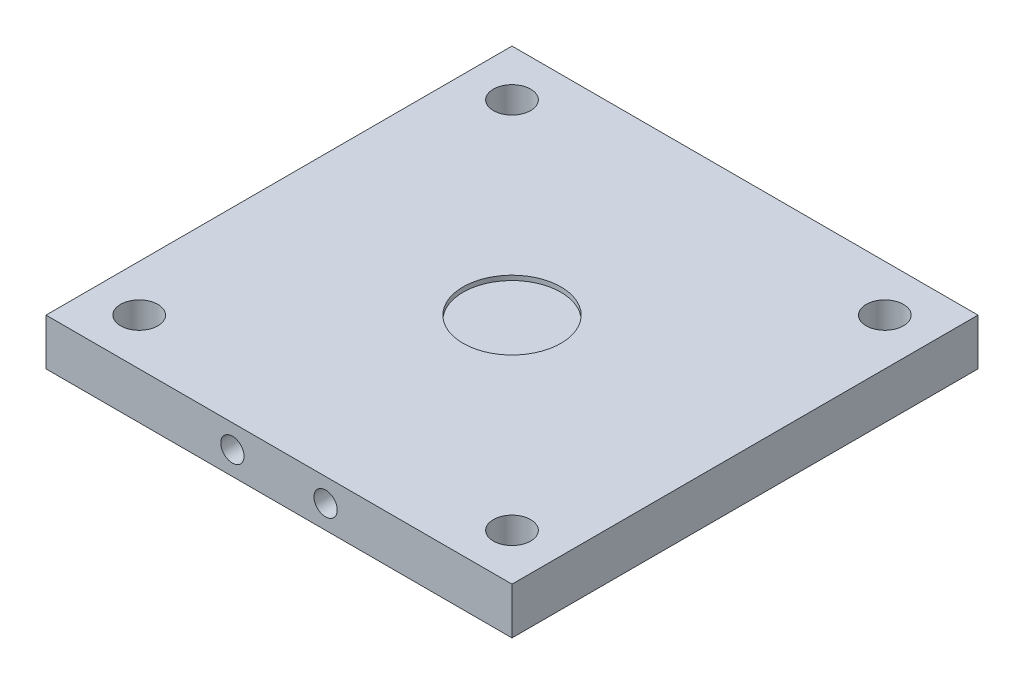
SolidWorks part; units mm, degrees
material "6061-T4 (SS)"
ref_plane "Front Plane" through (0, 0, 0) normal (0, 0, 1) x (1, 0, 0)
ref_plane "Top Plane" through (0, 0, 0) normal (0, 1, 0) x (1, 0, 0)
ref_plane "Right Plane" through (0, 0, 0) normal (1, 0, 0) x (0, 0, -1)
sketch "Sketch1" plane through (0, 0, 0) normal (0, 1, 0) x (1, 0, 0)
  line L1 (50, 50) -> (-50, 50)
  line L2 (50, 50) -> (50, -50)
  line L3 (50, -50) -> (-50, -50)
  line L4 (-50, 50) -> (-50, -50)
  line L5 (50, 50) -> (-50, -50) construction
  line L6 (50, -50) -> (-50, 50) construction
  point P0 (0, 0)
  dimension "D1" = 100
  dimension "D2" = 100
extrude "base" add sketch "Sketch1" along normal blind 10
sketch "Sketch2" plane through (0, 10, 0) normal (0, 1, 0) x (1, 0, 0)
  circle A0 centre (0, 0) radius 10.5
  dimension "D1" = 21
extrude "load cell cut" cut sketch "Sketch2" against normal blind 1 contours A0
sketch "post positioning points" plane through (0, 10, 0) normal (0, 1, 0) x (1, 0, 0)
  line L0 (-50, 50) -> (-50, -50) construction
  line L1 (-50, -50) -> (50, -50) construction
  line L2 (50, -50) -> (50, 50) construction
  line L3 (50, 50) -> (-50, 50) construction
  point P0 (-10, -40)
  point P5 (50, 40)
  point P6 (-10, 40)
  point P7 (10, 40)
  point P8 (10, -40)
  point P9 (75, -40)
  point P10 (-50, 40)
  dimension "D1" = 40
  dimension "D2" = 10
  dimension "D3" = 40
  dimension "D4" = 10
  dimension "D5" = 85
  dimension "D7" = 60
  dimension "D6" = 60
sketch "Sketch6" plane through (0, 0, -50) normal (0, 0, 1) x (1, 0, 0)
  line L0 (-50, 0) -> (50, 0) construction
  line L1 (9, 10) -> (-9, 10)
  line L2 (9, 10) -> (9, 5)
  line L3 (9, 5) -> (-9, 5)
  line L4 (-9, 10) -> (-9, 5)
  line L5 (9, 10) -> (-9, 5) construction
  line L6 (9, 5) -> (-9, 10) construction
  line L7 (-50, 10) -> (50, 10) construction
  point P0 (0, 7.5)
  point P8 (0, 0)
  dimension "D1" = 18
  dimension "D2" = 5
extrude "cut wire" [suppressed] cut sketch "Sketch6" along normal blind 50 contours L4 L3 L2 L1
sketch "Sketch7" plane through (0, 0, -50) normal (0, 0, 1) x (1, 0, 0)
  line L1 (5, 10) -> (-5, 10)
  line L2 (5, 10) -> (5, 0)
  line L3 (5, 0) -> (-5, 0)
  line L4 (-5, 10) -> (-5, 0)
  line L5 (5, 10) -> (-5, 0) construction
  line L6 (5, 0) -> (-5, 10) construction
  line L7 (-50, 0) -> (50, 0) construction
  line L8 (-50, 10) -> (50, 10) construction
  point P0 (0, 5)
  point P8 (0, 0)
  dimension "D1" = 10
  dimension "D2" = 10
extrude "cut wire 2" [suppressed] cut sketch "Sketch7" along normal up to next
fillet "Fillet5" [suppressed] radius 10
fillet "Fillet6" [suppressed] radius 0.1
fillet "Fillet7" [suppressed] radius 5
sketch "Sketch12" plane through (0, 0, 0) normal (0, -1, 0) x (1, 0, 0)
  line L0 (0, 0) -> (50, 0) construction
  line L1 (19.771, 8.1894) -> (-8.1894, 19.771) construction
  line L2 (-8.1894, 19.771) -> (-19.771, -8.1894) construction
  line L3 (-19.771, -8.1894) -> (8.1894, -19.771) construction
  line L4 (8.1894, -19.771) -> (19.771, 8.1894) construction
  line L5 (50, 50) -> (50, -50) construction
  circle A0 centre (0, 0) radius 15.1321 construction
  dimension "D1" = 22.5
  dimension "D2" = 21.4
hole_wizard "Ø5.0mm Dowel Hole1" [suppressed] positions "3DSketch4" profile "Sketch13" hole size "Ø5.0" standard "ANSI Metric"
sketch3d "3DSketch4"
  point P0 (-8.1894, 0, 19.771)
  point P3 (19.771, 0, 8.1894)
  point P6 (8.1894, 0, -19.771)
  point P9 (-19.771, 0, -8.1894)
sketch "Sketch13" plane through (-8.1894, 0, 19.771) normal (1, 0, 0) x (0, 0, -1)
  line L0 (0, 0) -> (0, 5)
  line L1 (0, 5) -> (2.5, 5)
  line L2 (2.5, 5) -> (2.5, 0)
  line L5 (2.5, 0) -> (0, 0)
  line L11 (0, -6.35) -> (0, 107.95) construction
  dimension "Thru Hole Dia." = 5
  dimension "Thru Hole Depth" = 5
fillet "Fillet8" [suppressed] radius 5
sketch "Sketch14" plane through (0, 9, 0) normal (0, 1, 0) x (1, 0, 0)
  circle A0 centre (0, 0) radius 25
  dimension "D1" = 50
split line "Split Line1" [suppressed]
fillet "Fillet9" [suppressed] radius 1
sketch "Sketch15" plane through (0, 0, 0) normal (0, -1, 0) x (-1, 0, 0)
  line L0 (-40, -40) -> (40, -40) construction
  line L1 (40, -40) -> (40, 40) construction
  circle A0 centre (40, -40) radius 3
  circle A1 centre (-40, -40) radius 3
  circle A2 centre (40, 40) radius 3
  circle A3 centre (-40, 40) radius 3
  point P2 (40, 0)
  point P5 (0, -40)
  dimension "D3" = 6
  dimension "D1" = 80
  dimension "D2" = 80
extrude "Cut-Extrude1" cut sketch "Sketch15" against normal up to next
hole_wizard "Ø4.0mm Dowel Hole1" [suppressed] positions "Sketch17" profile "Sketch18" hole size "Ø4.0" standard "ANSI Metric"
sketch "Sketch17" plane through (0, 0, 50) normal (0, 0, 1) x (1, 0, 0)
  line L1 (-50, 10) -> (-50, 0) construction
  line L2 (50, 10) -> (50, 0) construction
  point P0 (-45, 5)
  point P3 (-25, 5)
  point P6 (25, 5)
  point P9 (45, 5)
  dimension "D1" = 25
  dimension "D2" = 5
  dimension "D3" = 25
  dimension "D4" = 5
sketch "Sketch18" plane through (-45, 5, 50) normal (1, 0, 0) x (0, -1, 0)
  line L0 (0, 0) -> (0, 11.2017)
  line L1 (0, 11.2017) -> (2, 10)
  line L2 (2, 10) -> (2, 0)
  line L5 (2, 0) -> (0, 0)
  line L10 (0, 11.2017) -> (-2, 10) construction
  line L11 (0, -6.35) -> (0, 107.95) construction
  dimension "Hole Dia." = 4
  dimension "Hole Depth" = 10
  dimension "Drill Angle" = 118
cosmetic thread "Cosmetic Thread1" [suppressed] parameters "D2"=4
cosmetic thread "Cosmetic Thread2" [suppressed] parameters "D2"=5
cosmetic thread "Cosmetic Thread3" [suppressed] parameters "D2"=4
cosmetic thread "Cosmetic Thread4" [suppressed] parameters "D2"=4
cosmetic thread "Cosmetic Thread9" [suppressed] parameters "D2"=5
cosmetic thread "Cosmetic Thread11" [suppressed] parameters "D2"=5
cosmetic thread "Cosmetic Thread13" [suppressed] parameters "D2"=5
mirror "Mirror1" [suppressed] about plane through (0, 0, 0) normal (0, 0, 1)
cosmetic thread "Cosmetic Thread5" [suppressed] parameters "D2"=5
cosmetic thread "Cosmetic Thread6" [suppressed] parameters "D2"=4
cosmetic thread "Cosmetic Thread7" [suppressed] parameters "D2"=4
cosmetic thread "Cosmetic Thread8" [suppressed] parameters "D2"=4
cosmetic thread "Cosmetic Thread10" [suppressed] parameters "D2"=5
cosmetic thread "Cosmetic Thread12" [suppressed] parameters "D2"=5
cosmetic thread "Cosmetic Thread14" [suppressed] parameters "D2"=5
cosmetic thread "Cosmetic Thread15" [suppressed] parameters "D2"=5
cosmetic thread "Cosmetic Thread16" [suppressed] parameters "D2"=5
cosmetic thread "Cosmetic Thread17" [suppressed] parameters "D2"=5
cosmetic thread "Cosmetic Thread18" [suppressed] parameters "D2"=5
sketch "Sketch21" plane through (0, 0, -50) normal (0, 0, -1) x (-1, 0, 0)
  circle A0 centre (-10, 5) radius 2.5
  circle A1 centre (10, 5) radius 2.5
  dimension "D1" = 5
  dimension "D2" = 5
extrude "Cut-Extrude2" cut sketch "Sketch21" against normal blind 10
mirror "Mirror2" about plane through (0, 0, 0) normal (0, 0, 1) of "Cut-Extrude2"
sketch "Sketch22" plane through (0, 10, 0) normal (0, 1, 0) x (1, 0, 0)
  circle A0 centre (40, -40) radius 4
  circle A1 centre (-40, -40) radius 4
  circle A2 centre (-40, 40) radius 4
  circle A3 centre (40, 40) radius 4
  dimension "D1" = 8
extrude "Cut-Extrude3" cut sketch "Sketch22" against normal through all
equation "\"D2@post positioning points\"=10"
equation "\"D3@post positioning points\"=\"D1@post positioning points\""
equation "\"D4@post positioning points\"=\"D2@post positioning points\""
equation "\"D1@base\"=10"
equation "\"D1@load cell cut\"=5"
equation "\"D2@Sketch6\"=5"
